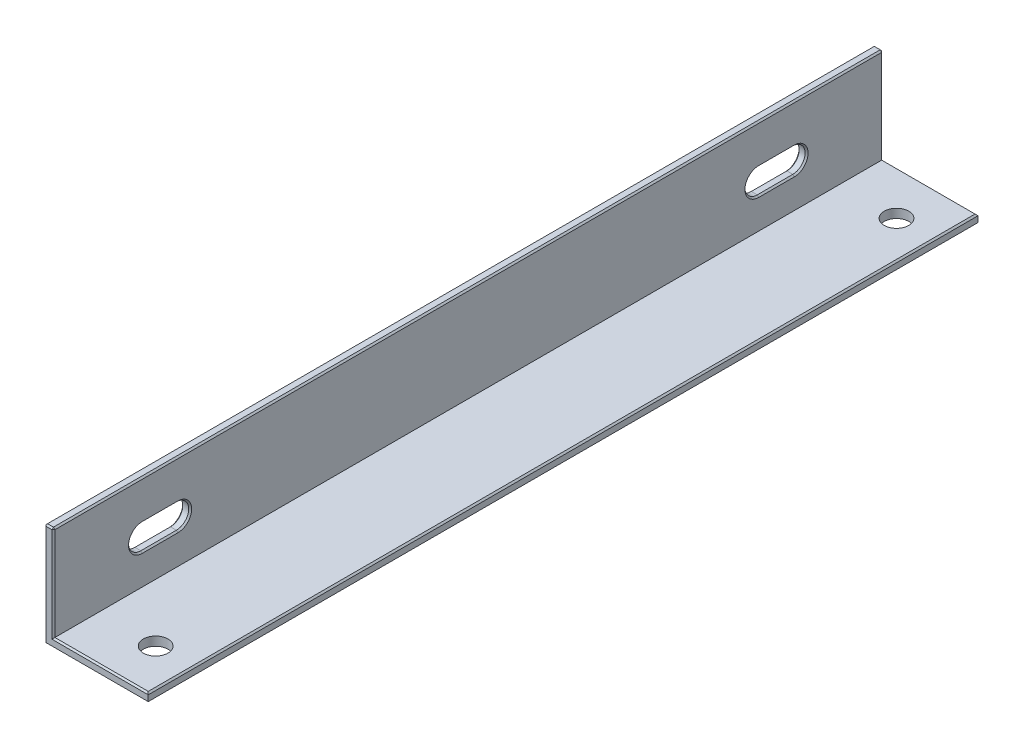
SolidWorks part; units mm, degrees
ref_plane "Přední rovina" through (0, 0, 0) normal (0, 0, 1) x (1, 0, 0)
ref_plane "Horní rovina" through (0, 0, 0) normal (0, 1, 0) x (1, 0, 0)
ref_plane "Pravá rovina" through (0, 0, 0) normal (1, 0, 0) x (0, 0, -1)
sketch "Skica1" plane through (0, 0, 0) normal (0, 0, 1) x (1, 0, 0)
  line L0 (0, 35) -> (0, 0)
  line L1 (0, 0) -> (35, 0)
  line L2 (35, 0) -> (35, 3)
  line L3 (35, 3) -> (3, 3)
  line L4 (3, 3) -> (3, 35)
  line L5 (3, 35) -> (0, 35)
  dimension "D1" = 35
  dimension "D2" = 35
  dimension "D3" = 3
  dimension "D4" = 3
extrude "Přidat vysunutím1" add sketch "Skica1" along normal blind 280
ref_plane "Rovina1" through (0, 0, 0) normal (-1, 0, 0) x (0, 0, 1)
sketch "Skica2" plane through (0, 0, 0) normal (-1, 0, 0) x (0, 0, 1)
  line L0 (0, 17.5) -> (280, 17.5) construction
  line L1 (0, 35) -> (0, 0) construction
  line L2 (280, 35) -> (280, 0) construction
  line L3 (30, 21.65) -> (42, 21.65)
  line L4 (238, 21.65) -> (250, 21.65)
  line L5 (250, 13.35) -> (238, 13.35)
  line L6 (42, 13.35) -> (30, 13.35)
  arc A0 (30, 13.35) -> (30, 21.65) centre (30, 17.5) cw
  arc A1 (42, 21.65) -> (42, 13.35) centre (42, 17.5) cw
  arc A2 (238, 21.65) -> (238, 13.35) centre (238, 17.5) ccw
  arc A3 (250, 21.65) -> (250, 13.35) centre (250, 17.5) cw
  dimension "D1" = 4.15
  dimension "D3" = 4.15
  dimension "D4" = 4.15
  dimension "D5" = 4.15
  dimension "D2" = 30
  dimension "D6" = 30
  dimension "D7" = 12
  dimension "D8" = 12
extrude "Odebrat vysunutím1" cut sketch "Skica2" against normal blind 4
ref_plane "Rovina2" through (0, 3, 0) normal (0, 1, 0) x (-1, 0, 0)
sketch "Skica3" plane through (0, 3, 0) normal (0, 1, 0) x (-1, 0, 0)
  line L0 (-22.5, 280) -> (-22.5, 0) construction
  line L1 (-35, 280) -> (-3, 280) construction
  line L2 (-35, 0) -> (-3, 0) construction
  line L3 (-35, 280) -> (-35, 0) construction
  circle A0 centre (-22.5, 265) radius 4.15
  circle A1 centre (-22.5, 15) radius 4.15
  dimension "D2" = 8.3
  dimension "D3" = 8.3
  dimension "D1" = 12.5
  dimension "D4" = 250
  dimension "D5" = 15
extrude "Odebrat vysunutím2" cut sketch "Skica3" against normal blind 4
chamfer "Zkosení1" distance 0.5 angle 45 29 edges at (3, 17.5, 25.85) (3, 13.35, 36) (3, 21.65, 36) (3, 17.5, 46.15) (3, 17.5, 233.85) (3, 21.65, 244) (3, 17.5, 254.15) (3, 13.35, 244) (3, 19, 280) (19, 3, 280) (35, 3, 140) (19, 3, 0) (3, 19, 0) (17.5, 0, 280) (35, 0, 140) (17.5, 0, 0) (0, 17.5, 0) (1.5, 35, 0) (3, 35, 140) (1.5, 35, 280) (0, 17.5, 280) (0, 17.5, 25.85) (0, 21.65, 36) (0, 17.5, 46.15) (0, 13.35, 36) (0, 17.5, 233.85) (0, 21.65, 244) (0, 17.5, 254.15) (0, 13.35, 244)
chamfer "Zkosení2" distance 0.5 angle 45 1 edges at (0, 35, 140)
